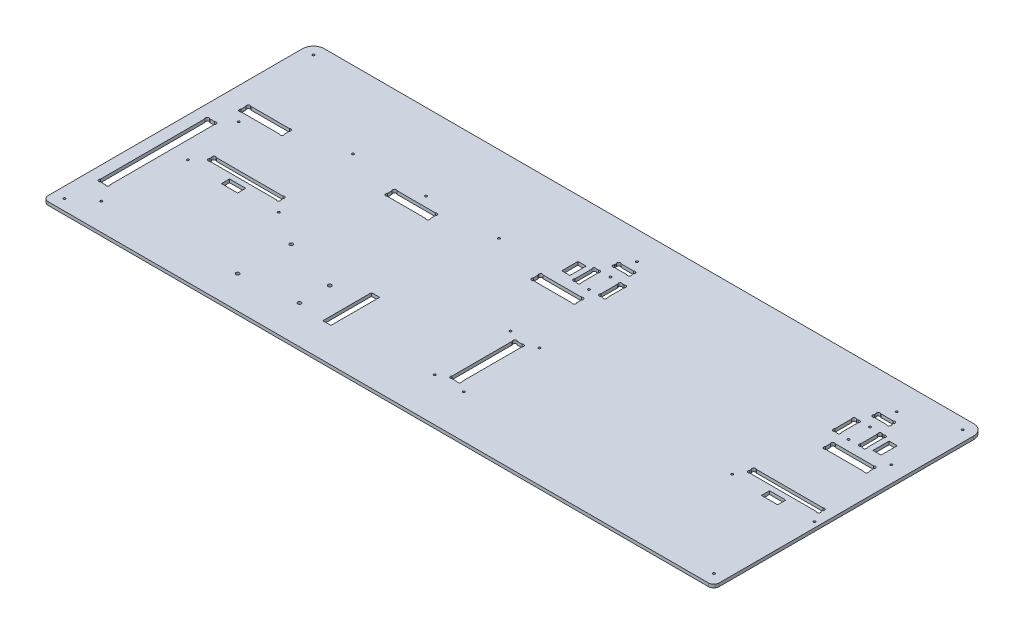
SolidWorks part; units mm, degrees
ref_plane "Plan de face" through (0, 0, 0) normal (0, 0, 1) x (1, 0, 0)
ref_plane "Plan de dessus" through (0, 0, 0) normal (0, 1, 0) x (1, 0, 0)
ref_plane "Plan de droite" through (0, 0, 0) normal (1, 0, 0) x (0, 0, -1)
sketch "Esquisse1" plane through (0, 0, 0) normal (0, 1, 0) x (1, 0, 0)
  line L26 (317, 211.2627) -> (317, 212.7373)
  line L28 (319.2627, 215) -> (330.7373, 215)
  line L29 (333, 211.2627) -> (333, 212.7373)
  line L30 (330.7373, 209) -> (319.2627, 209)
  line L31 (312.2627, 179.5) -> (313.7373, 179.5)
  line L32 (312.2627, 199.5) -> (313.7373, 199.5)
  line L33 (310, 197.2373) -> (310, 181.7627)
  line L34 (316, 181.7627) -> (316, 197.2373)
  line L35 (334, 181.7627) -> (334, 197.2373)
  line L36 (340, 197.2373) -> (340, 181.7627)
  line L37 (337.7373, 199.5) -> (336.2627, 199.5)
  line L38 (337.7373, 179.5) -> (336.2627, 179.5)
  line L39 (552.2627, 179.5) -> (553.7373, 179.5)
  line L40 (552.2627, 199.5) -> (553.7373, 199.5)
  line L41 (550, 197.2373) -> (550, 181.7627)
  line L42 (556, 181.7627) -> (556, 197.2373)
  line L43 (574, 181.7627) -> (574, 197.2373)
  line L44 (580, 197.2373) -> (580, 181.7627)
  line L45 (577.7373, 199.5) -> (576.2627, 199.5)
  line L46 (577.7373, 179.5) -> (576.2627, 179.5)
  line L47 (559.2627, 209) -> (570.7373, 209)
  line L48 (557, 211.2627) -> (557, 212.7373)
  line L49 (570.7373, 215) -> (559.2627, 215)
  line L50 (573, 211.2627) -> (573, 212.7373)
  line L55 (560, 167.7373) -> (560, 163.2627)
  line L56 (600, 167.7373) -> (600, 163.2627)
  line L57 (562.2627, 170) -> (597.7373, 170)
  line L58 (597.7373, 161) -> (562.2627, 161)
  line L59 (292.2627, 161) -> (327.7373, 161)
  line L60 (327.7373, 170) -> (292.2627, 170)
  line L61 (290, 167.7373) -> (290, 163.2627)
  line L62 (330, 167.7373) -> (330, 163.2627)
  line L64 (20, 167.7373) -> (20, 163.2627)
  line L65 (60, 167.7373) -> (60, 163.2627)
  line L66 (22.2627, 170) -> (57.7373, 170)
  line L67 (57.7373, 161) -> (22.2627, 161)
  line L70 (155, 167.7373) -> (155, 163.2627)
  line L71 (195, 167.7373) -> (195, 163.2627)
  line L72 (157.2627, 170) -> (192.7373, 170)
  line L73 (192.7373, 161) -> (157.2627, 161)
  line L76 (10, 250) -> (610, 250)
  line L77 (0, 240) -> (0, 0)
  line L78 (0, 0) -> (620, 0)
  line L79 (620, 240) -> (620, 0)
  line L84 (13.2627, 40) -> (17.7373, 40)
  line L85 (13.2627, 141) -> (17.7373, 141)
  line L86 (11, 138.7373) -> (11, 42.2627)
  line L87 (20, 42.2627) -> (20, 138.7373)
  line L98 (337.7373, 45) -> (333.2627, 45)
  line L99 (337.7373, 105) -> (333.2627, 105)
  line L100 (340, 47.2627) -> (340, 102.7373)
  line L101 (331, 102.7373) -> (331, 47.2627)
  line L109 (610, 109.2627) -> (610, 110.7373)
  line L110 (544, 109.2627) -> (544, 110.7373)
  line L111 (607.7373, 107) -> (546.2627, 107)
  line L112 (546.2627, 113) -> (607.7373, 113)
  line L113 (108.7373, 113) -> (47.2627, 113)
  line L114 (47.2627, 107) -> (108.7373, 107)
  line L115 (111, 109.2627) -> (111, 110.7373)
  line L116 (45, 109.2627) -> (45, 110.7373)
  arc A0 (319.2627, 215) -> (317, 212.7373) centre (318.1314, 213.8686) ccw
  arc A1 (319.2627, 209) -> (317, 211.2627) centre (318.1314, 210.1314) cw
  arc A2 (330.7373, 209) -> (333, 211.2627) centre (331.8686, 210.1314) ccw
  arc A3 (330.7373, 215) -> (333, 212.7373) centre (331.8686, 213.8686) cw
  arc A4 (313.7373, 179.5) -> (316, 181.7627) centre (314.8686, 180.6314) ccw
  arc A5 (312.2627, 179.5) -> (310, 181.7627) centre (311.1314, 180.6314) cw
  arc A6 (312.2627, 199.5) -> (310, 197.2373) centre (311.1314, 198.3686) ccw
  arc A7 (313.7373, 199.5) -> (316, 197.2373) centre (314.8686, 198.3686) cw
  arc A8 (336.2627, 179.5) -> (334, 181.7627) centre (335.1314, 180.6314) cw
  arc A9 (336.2627, 199.5) -> (334, 197.2373) centre (335.1314, 198.3686) ccw
  arc A10 (337.7373, 199.5) -> (340, 197.2373) centre (338.8686, 198.3686) cw
  arc A11 (337.7373, 179.5) -> (340, 181.7627) centre (338.8686, 180.6314) ccw
  arc A12 (552.2627, 179.5) -> (550, 181.7627) centre (551.1314, 180.6314) cw
  arc A13 (552.2627, 199.5) -> (550, 197.2373) centre (551.1314, 198.3686) ccw
  arc A14 (553.7373, 199.5) -> (556, 197.2373) centre (554.8686, 198.3686) cw
  arc A15 (553.7373, 179.5) -> (556, 181.7627) centre (554.8686, 180.6314) ccw
  arc A16 (576.2627, 199.5) -> (574, 197.2373) centre (575.1314, 198.3686) ccw
  arc A17 (577.7373, 199.5) -> (580, 197.2373) centre (578.8686, 198.3686) cw
  arc A18 (577.7373, 179.5) -> (580, 181.7627) centre (578.8686, 180.6314) ccw
  arc A19 (576.2627, 179.5) -> (574, 181.7627) centre (575.1314, 180.6314) cw
  arc A20 (559.2627, 215) -> (557, 212.7373) centre (558.1314, 213.8686) ccw
  arc A21 (559.2627, 209) -> (557, 211.2627) centre (558.1314, 210.1314) cw
  arc A22 (570.7373, 209) -> (573, 211.2627) centre (571.8686, 210.1314) ccw
  arc A23 (570.7373, 215) -> (573, 212.7373) centre (571.8686, 213.8686) cw
  arc A29 (560, 163.2627) -> (562.2627, 161) centre (561.1314, 162.1314) ccw
  arc A30 (560, 167.7373) -> (562.2627, 170) centre (561.1314, 168.8686) cw
  arc A31 (600, 167.7373) -> (597.7373, 170) centre (598.8686, 168.8686) ccw
  arc A32 (600, 163.2627) -> (597.7373, 161) centre (598.8686, 162.1314) cw
  arc A34 (290, 163.2627) -> (292.2627, 161) centre (291.1314, 162.1314) ccw
  arc A35 (290, 167.7373) -> (292.2627, 170) centre (291.1314, 168.8686) cw
  arc A36 (330, 167.7373) -> (327.7373, 170) centre (328.8686, 168.8686) ccw
  arc A37 (330, 163.2627) -> (327.7373, 161) centre (328.8686, 162.1314) cw
  arc A40 (20, 163.2627) -> (22.2627, 161) centre (21.1314, 162.1314) ccw
  arc A41 (20, 167.7373) -> (22.2627, 170) centre (21.1314, 168.8686) cw
  arc A42 (60, 167.7373) -> (57.7373, 170) centre (58.8686, 168.8686) ccw
  arc A43 (60, 163.2627) -> (57.7373, 161) centre (58.8686, 162.1314) cw
  arc A44 (155, 163.2627) -> (157.2627, 161) centre (156.1314, 162.1314) ccw
  arc A45 (155, 167.7373) -> (157.2627, 170) centre (156.1314, 168.8686) cw
  arc A46 (195, 163.2627) -> (192.7373, 161) centre (193.8686, 162.1314) cw
  arc A47 (195, 167.7373) -> (192.7373, 170) centre (193.8686, 168.8686) ccw
  arc A50 (17.7373, 40) -> (20, 42.2627) centre (18.8686, 41.1314) ccw
  arc A52 (13.2627, 40) -> (11, 42.2627) centre (12.1314, 41.1314) cw
  arc A53 (17.7373, 141) -> (20, 138.7373) centre (18.8686, 139.8686) cw
  arc A54 (13.2627, 141) -> (11, 138.7373) centre (12.1314, 139.8686) ccw
  arc A56 (10, 250) -> (0, 240) centre (10, 240) ccw
  arc A57 (610, 250) -> (620, 240) centre (610, 240) cw
  arc A59 (331, 47.2627) -> (333.2627, 45) centre (332.1314, 46.1314) ccw
  arc A60 (340, 47.2627) -> (337.7373, 45) centre (338.8686, 46.1314) cw
  arc A61 (331, 102.7373) -> (333.2627, 105) centre (332.1314, 103.8686) cw
  arc A62 (340, 102.7373) -> (337.7373, 105) centre (338.8686, 103.8686) ccw
  arc A64 (607.7373, 107) -> (610, 109.2627) centre (608.8686, 108.1314) ccw
  circle A65 centre (539, 98) radius 1
  arc A66 (607.7373, 113) -> (610, 110.7373) centre (608.8686, 111.8686) cw
  circle A67 centre (615, 98) radius 1
  arc A68 (546.2627, 113) -> (544, 110.7373) centre (545.1314, 111.8686) ccw
  arc A69 (546.2627, 107) -> (544, 109.2627) centre (545.1314, 108.1314) cw
  arc A70 (108.7373, 107) -> (111, 109.2627) centre (109.8686, 108.1314) ccw
  arc A71 (108.7373, 113) -> (111, 110.7373) centre (109.8686, 111.8686) cw
  arc A73 (47.2627, 113) -> (45, 110.7373) centre (46.1314, 111.8686) ccw
  arc A75 (47.2627, 107) -> (45, 109.2627) centre (46.1314, 108.1314) cw
  point P1 (337, 199.5)
  point P7 (340, 189.5)
  dimension "D25" = 6
  dimension "D28" = 16
  dimension "D29" = 20
  dimension "D32" = 9.5
  dimension "D33" = 35
  dimension "D39" = 10
  dimension "D49" = 1.1314
  dimension "D57" = 6
  dimension "D55" = 10
  dimension "D62" = 5
  dimension "D63" = 1.6
  dimension "D64" = 9
  dimension "D65" = 1.1314
  dimension "D66" = 1.1314
  dimension "D67" = 620
  dimension "D9" = 2.2627
  dimension "D10" = 1.6
  dimension "D78" = 3.7373
  dimension "D14" = 1.6
  dimension "D36" = 1.6
  dimension "D61" = 1.6
  dimension "D95" = 1.6
  dimension "D107" = 1.6
  dimension "D118" = 1.6
  dimension "D119" = 1.6
  dimension "D128" = 6
  dimension "D141" = 1.6
  dimension "D58" = 2
  dimension "D2" = 250
  dimension "D8" = 20
  dimension "D13" = 40
  dimension "D16" = 1.1314
  dimension "D17" = 1.1314
  dimension "D19" = 2.2627
  dimension "D20" = 2.2627
  dimension "D21" = 80
  dimension "D22" = 9
  dimension "D23" = 1.1314
  dimension "D24" = 1.1314
  dimension "D26" = 6
  dimension "D27" = 6
  dimension "D30" = 40
  dimension "D31" = 18
  dimension "D37" = 1.1314
  dimension "D38" = 2.2627
  dimension "D40" = 1.1314
  dimension "D41" = 1.1314
  dimension "D42" = 1.1314
  dimension "D43" = 1.1314
  dimension "D45" = 1
  dimension "D46" = 1.1314
  dimension "D47" = 1.1314
  dimension "D48" = 1.1314
  dimension "D51" = 3.7373
  dimension "D52" = 66
  dimension "D53" = 10
  dimension "D54" = 66
  dimension "D56" = 107
  dimension "D59" = 1.1314
  dimension "D60" = 2.2627
  dimension "D68" = 60
  dimension "D70" = 6
  dimension "D72" = 1.1314
  dimension "D73" = 1.1314
  dimension "D74" = 63.7373
  dimension "D75" = 2.2627
  dimension "D76" = 2.2627
  dimension "D77" = 45
  dimension "D79" = 45
  dimension "D83" = 280
  dimension "D84" = 1.1314
  dimension "D85" = 1.1314
  dimension "D86" = 1.1314
  dimension "D87" = 1.1314
  dimension "D88" = 9
  dimension "D89" = 101
  dimension "D90" = 40
  dimension "D91" = 11
  dimension "D96" = 1.1314
  dimension "D97" = 1.1314
  dimension "D98" = 1.1314
  dimension "D100" = 1.1314
  dimension "D105" = 9
  dimension "D106" = 40
  dimension "D108" = 20
  dimension "D109" = 80
  dimension "D110" = 1.1314
  dimension "D111" = 1.1314
  dimension "D112" = 1.1314
  dimension "D113" = 1.1314
  dimension "D114" = 40
  dimension "D115" = 95
  dimension "D116" = 95
  dimension "D117" = 40
  dimension "D120" = 1.1314
  dimension "D121" = 1.1314
  dimension "D122" = 1.1314
  dimension "D123" = 1.1314
  dimension "D124" = 1.1314
  dimension "D125" = 1.1314
  dimension "D126" = 1.1314
  dimension "D127" = 1.1314
  dimension "D129" = 6
  dimension "D130" = 6
  dimension "D132" = 20
  dimension "D133" = 16
  dimension "D135" = 35
  dimension "D136" = 9.5
  dimension "D139" = 1
  dimension "D140" = 18
  dimension "D142" = 1.1314
  dimension "D143" = 1.1314
  dimension "D144" = 1.1314
  dimension "D145" = 1.1314
  dimension "D146" = 1.1314
  dimension "D147" = 1.1314
  dimension "D148" = 1.1314
  dimension "D149" = 1.1314
  dimension "D150" = 1.1314
  dimension "D151" = 1.1314
  dimension "D152" = 1.1314
  dimension "D153" = 1.1314
  dimension "D154" = 9
  dimension "D155" = 5
extrude "Extrusion1" add sketch "Esquisse1" along normal blind 3
sketch "Esquisse2" plane through (0, 3, 0) normal (0, 1, 0) x (-1, 0, 0)
  line L0 (-610, -250) -> (-10, -250) construction
  line L5 (-620, 21.4973) -> (-620, -261.3021) construction
  line L7 (-573, -142.8) -> (-72, -142.8)
  line L8 (-573, -142.8) -> (-573, -147)
  line L9 (-573, -147) -> (-72, -147)
  line L10 (-72, -142.8) -> (-72, -147)
  dimension "D1" = 47
  dimension "D2" = 4.2
  dimension "D3" = 501
  dimension "D4" = 103
extrude "Enlèv. mat.-Extru.1" [suppressed] cut sketch "Esquisse2" against normal through all
sketch "Esquisse3" plane through (0, 3, 0) normal (0, 1, 0) x (1, 0, 0)
  line L0 (574, 197.2373) -> (574, 181.7627) construction
  line L1 (556, 181.7627) -> (556, 197.2373) construction
  line L2 (559.2627, 209) -> (570.7373, 209) construction
  line L4 (576.2627, 179.5) -> (577.7373, 179.5) construction
  line L5 (577.7373, 199.5) -> (576.2627, 199.5) construction
  line L6 (334, 197.2373) -> (334, 181.7627) construction
  circle A0 centre (565, 179.5) radius 1
  circle A1 centre (565, 199.5) radius 1
  circle A2 centre (325, 179.5) radius 1
  circle A3 centre (325, 199.5) radius 1
  dimension "D1" = 2
  dimension "D2" = 9
  dimension "D3" = 9
  dimension "D4" = 20
  dimension "D5" = 9.5
  dimension "D6" = 0
  dimension "D7" = 0
  dimension "D8" = 9
extrude "Enlèv. mat.-Extru.2" cut sketch "Esquisse3" against normal through all
fillet "Congé1" radius 5 2 edges at (620, 1.5, 0) (0, 1.5, 0)
sketch "Esquisse4" plane through (0, 0, 0) normal (0, -1, 0) x (1, 0, 0)
  line L0 (0, -240) -> (0, -5) construction
  line L1 (5, 0) -> (615, 0) construction
  line L2 (610, -250) -> (10, -250) construction
  line L3 (620, -5) -> (620, -240) construction
  circle A0 centre (10, -10) radius 1
  circle A1 centre (610, -10) radius 1
  circle A2 centre (610, -240) radius 1
  circle A3 centre (10, -240) radius 1
  dimension "D1" = 2
  dimension "D2" = 10
  dimension "D3" = 10
  dimension "D4" = 10
  dimension "D5" = 10
  dimension "D6" = 10
  dimension "D7" = 10
  dimension "D8" = 10
  dimension "D9" = 10
extrude "Enlèv. mat.-Extru.3" cut sketch "Esquisse4" against normal through all
sketch "Esquisse5" plane through (0, 3, 0) normal (0, 1, 0) x (1, 0, 0)
  line L1 (0, 240) -> (0, 5) construction
  line L2 (5, 0) -> (615, 0) construction
  circle A0 centre (151.27, 78.26) radius 1.59
  circle A1 centre (150, 30) radius 1.59
  circle A2 centre (202.07, 63.02) radius 1.59
  circle A3 centre (202.07, 35.08) radius 1.59
  dimension "D1" = 3.18
  dimension "D7" = 30
  dimension "D2" = 48.26
  dimension "D3" = 27.94
  dimension "D4" = 52.07
  dimension "D5" = 5.08
  dimension "D6" = 150
  dimension "D8" = 1.27
extrude "Enlèv. mat.-Extru.4" cut sketch "Esquisse5" against normal through all
sketch "Esquisse6" plane through (0, 3, 0) normal (0, 1, 0) x (1, 0, 0)
  line L0 (544, 110.7373) -> (544, 109.2627) construction
  line L1 (569.5, 102) -> (584.5, 102)
  line L2 (569.5, 102) -> (569.5, 94.5)
  line L3 (569.5, 94.5) -> (584.5, 94.5)
  line L4 (584.5, 102) -> (584.5, 94.5)
  line L5 (610, 109.2627) -> (610, 110.7373) construction
  line L6 (546.2627, 107) -> (607.7373, 107) construction
  line L8 (585, 197) -> (592.5, 197)
  line L9 (585, 197) -> (585, 182)
  line L10 (585, 182) -> (592.5, 182)
  line L11 (592.5, 197) -> (592.5, 182)
  line L12 (305, 197) -> (297.5, 197)
  line L13 (305, 197) -> (305, 182)
  line L14 (305, 182) -> (297.5, 182)
  line L15 (297.5, 197) -> (297.5, 182)
  line L16 (577.7373, 199.5) -> (576.2627, 199.5) construction
  line L17 (576.2627, 179.5) -> (577.7373, 179.5) construction
  line L18 (580, 181.7627) -> (580, 197.2373) construction
  line L19 (310, 197.2373) -> (310, 181.7627) construction
  line L20 (313.7373, 199.5) -> (312.2627, 199.5) construction
  line L21 (45, 110.7373) -> (45, 109.2627) construction
  line L22 (227.07, 76.63) -> (234.57, 76.63)
  line L23 (227.07, 76.63) -> (227.07, 31.63)
  line L24 (227.07, 31.63) -> (234.57, 31.63)
  line L25 (234.57, 76.63) -> (234.57, 31.63)
  line L26 (70.5, 102) -> (85.5, 102)
  line L27 (70.5, 102) -> (70.5, 94.5)
  line L28 (70.5, 94.5) -> (85.5, 94.5)
  line L29 (85.5, 102) -> (85.5, 94.5)
  circle A0 centre (150, 30) radius 1.59 construction
  circle A1 centre (151.27, 78.26) radius 1.59 construction
  circle A2 centre (202.07, 63.02) radius 1.59 construction
  dimension "D1" = 15
  dimension "D2" = 7.5
  dimension "D3" = 25.5
  dimension "D4" = 25.5
  dimension "D5" = 5
  dimension "D6" = 7.5
  dimension "D7" = 15
  dimension "D8" = 15
  dimension "D9" = 7.5
  dimension "D10" = 2.5
  dimension "D11" = 2.5
  dimension "D12" = 5
  dimension "D13" = 5
  dimension "D14" = 2.5
  dimension "D15" = 7.5
  dimension "D16" = 45
  dimension "D17" = 1.63
  dimension "D18" = 1.63
  dimension "D19" = 25
  dimension "D20" = 15
  dimension "D21" = 25.5
extrude "Enlèv. mat.-Extru.5" cut sketch "Esquisse6" against normal through all
sketch "Esquisse7" plane through (0, 3, 0) normal (0, 1, 0) x (1, 0, 0)
  line L1 (5, 0) -> (615, 0) construction
  line L2 (331, 102.7373) -> (331, 47.2627) construction
  line L3 (340, 47.2627) -> (340, 102.7373) construction
  line L4 (570.7373, 215) -> (559.2627, 215) construction
  line L5 (330.7373, 215) -> (319.2627, 215) construction
  line L6 (597.7373, 170) -> (562.2627, 170) construction
  line L7 (192.7373, 170) -> (157.2627, 170) construction
  line L8 (0, 240) -> (0, 5) construction
  line L10 (47.2627, 107) -> (108.7373, 107) construction
  line L11 (45, 110.7373) -> (45, 109.2627) construction
  line L12 (111, 109.2627) -> (111, 110.7373) construction
  circle A0 centre (349, 110) radius 1
  circle A1 centre (349, 40) radius 1
  circle A2 centre (322, 110) radius 1
  circle A3 centre (322, 40) radius 1
  circle A4 centre (605, 179) radius 1
  circle A5 centre (565, 224) radius 1
  circle A6 centre (325, 224) radius 1
  circle A7 centre (175, 179) radius 1
  circle A8 centre (242.5, 179) radius 1
  circle A9 centre (107.5, 179) radius 1
  circle A10 centre (120, 98) radius 1
  circle A11 centre (36, 98) radius 1
  circle A12 centre (29, 152) radius 1
  circle A13 centre (29, 25) radius 1
  point P34 (325, 215)
  point P35 (0, 0)
  point P38 (565, 215)
  point P39 (0, 0)
  point P42 (0, 0)
  point P47 (175, 170)
  point P48 (0, 0)
  point P53 (0, 0)
  point P58 (0, 0)
  dimension "D1" = 2
  dimension "D2" = 40
  dimension "D3" = 9
  dimension "D4" = 9
  dimension "D5" = 70
  dimension "D6" = 9
  dimension "D7" = 40
  dimension "D8" = 9
  dimension "D9" = 9
  dimension "D10" = 67.5
  dimension "D11" = 67.5
  dimension "D12" = 127
  dimension "D13" = 25
  dimension "D14" = 29
  dimension "D15" = 9
  dimension "D16" = 9
  dimension "D17" = 9
extrude "Enlèv. mat.-Extru.6" cut sketch "Esquisse7" against normal through all
